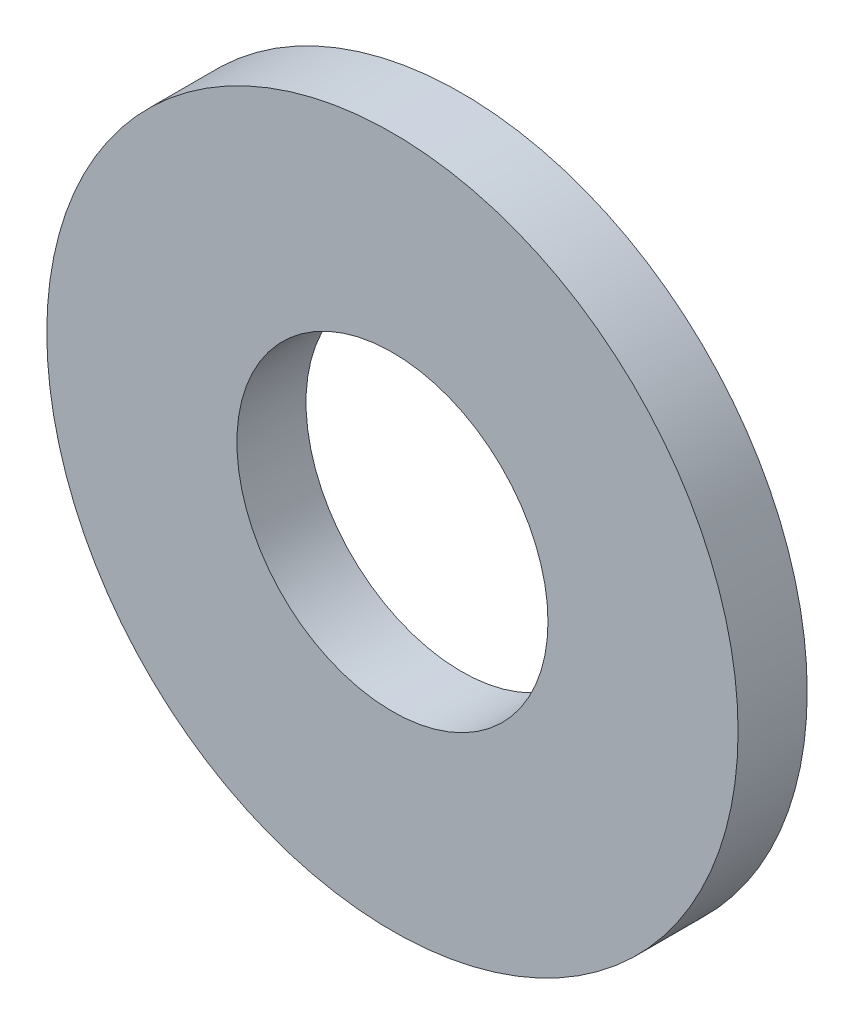
SolidWorks part; units mm, degrees
material "Alloy Steel (SS)"
ref_plane "Front Plane" through (0, 0, 0) normal (0, 0, 1) x (1, 0, 0)
ref_plane "Top Plane" through (0, 0, 0) normal (0, 1, 0) x (1, 0, 0)
ref_plane "Right Plane" through (0, 0, 0) normal (1, 0, 0) x (0, 0, -1)
sketch "Sketch1" plane through (0, 0, 0) normal (0, 0, 1) x (1, 0, 0)
  circle A0 centre (0, 0) radius 3
  circle A1 centre (0, 0) radius 1.35
  dimension "OD" = 6
  dimension "ID1" = 2.7
extrude "Boss-Extrude1" add sketch "Sketch1" along normal blind 0.6
